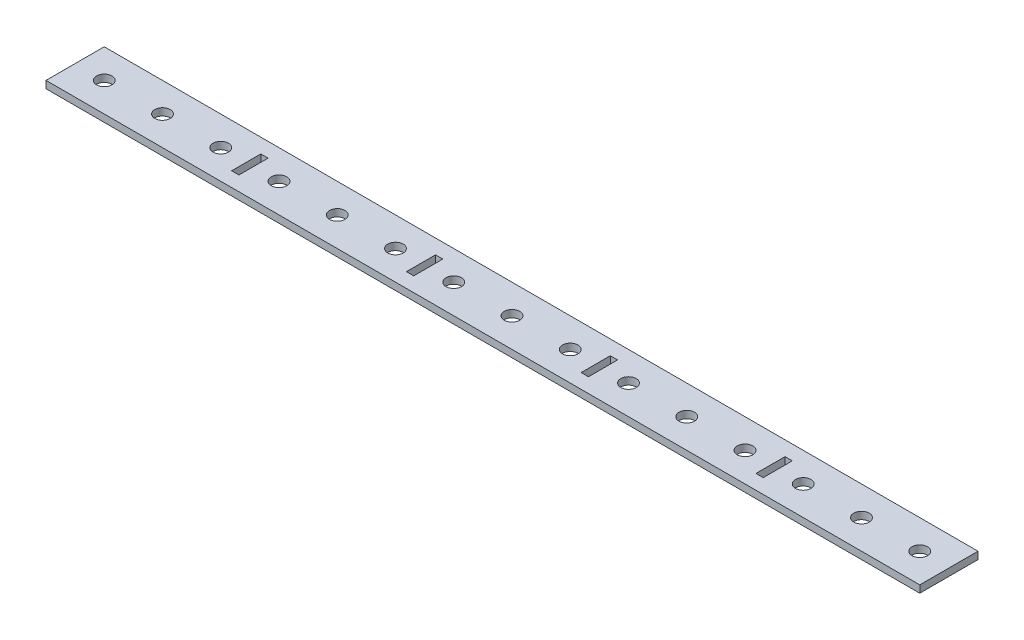
SolidWorks part; units mm, degrees
material "AISI 4340 Steel, annealed"
ref_plane "Front Plane" through (0, 0, 0) normal (0, 0, 1) x (1, 0, 0)
ref_plane "Top Plane" through (0, 0, 0) normal (0, 1, 0) x (1, 0, 0)
ref_plane "Right Plane" through (0, 0, 0) normal (1, 0, 0) x (0, 0, -1)
sketch "Sketch1" plane through (0, 0, 0) normal (0, 1, 0) x (1, 0, 0)
  line L1 (0, 0) -> (381, 0)
  line L2 (0, 0) -> (0, 25.4)
  line L3 (0, 25.4) -> (381, 25.4)
  line L4 (381, 0) -> (381, 25.4)
  dimension "D1" = 25.4
  dimension "14" = 381
extrude "Boss-Extrude1" add sketch "Sketch1" along normal blind 3.175
sketch "Pedalbox First Mounting Hole Location" plane through (0, 3.175, 0) normal (0, 1, 0) x (1, 0, 0)
  line L0 (0, 0) -> (381, 0) construction
  line L1 (0, 25.4) -> (0, 0) construction
  point P0 (12.7, 12.7)
  point P5 (35.5434, 12.7)
  dimension "D1" = 12.7
  dimension "D2" = 12.7
hole_wizard "1/4 Clearance First Mounting Hole" positions "Sketch6" profile "Sketch7" hole size "1/4" standard "ANSI Inch" end condition through all
sketch "Sketch6" plane through (0, 3.175, 0) normal (0, 1, 0) x (1, 0, 0)
  point P0 (12.7, 12.7)
sketch "Sketch7" plane through (12.7, 3.175, -12.7) normal (1, 0, 0) x (0, 0, 1)
  line L0 (0, 0) -> (0, 3.175)
  line L1 (0, 3.175) -> (3.3782, 3.175)
  line L2 (3.3782, 3.175) -> (3.3782, 0)
  line L5 (3.3782, 0) -> (0, 0)
  line L11 (0, -6.35) -> (0, 107.95) construction
  dimension "Thru Hole Dia." = 6.7564
  dimension "Thru Hole Depth" = 3.175
pattern_linear "Pedal Box Mounting Hole Pattern" count 15 spacing 25.4 along (1, 0, 0) of "1/4 Clearance First Mounting Hole"
sketch "Sketch8" plane through (0, 3.175, 0) normal (0, 1, 0) x (1, 0, 0)
  line L0 (0, 25.4) -> (0, 0) construction
  line L1 (74.6125, 19.05) -> (77.7875, 19.05)
  line L2 (74.6125, 19.05) -> (74.6125, 6.35)
  line L3 (74.6125, 6.35) -> (77.7875, 6.35)
  line L4 (77.7875, 19.05) -> (77.7875, 6.35)
  line L5 (0, 0) -> (381, 0) construction
  point P6 (76.2, 6.35)
  dimension "D1" = 3.175
  dimension "D2" = 12.7
  dimension "D3" = 74.6125
  dimension "D4" = 6.35
extrude "Support Tab Welding Cut" cut sketch "Sketch8" against normal blind 3.175
pattern_linear "Support Tab Welding Cut Pattern" count 4 spacing 76.2 along (1, 0, 0) of "Support Tab Welding Cut"
